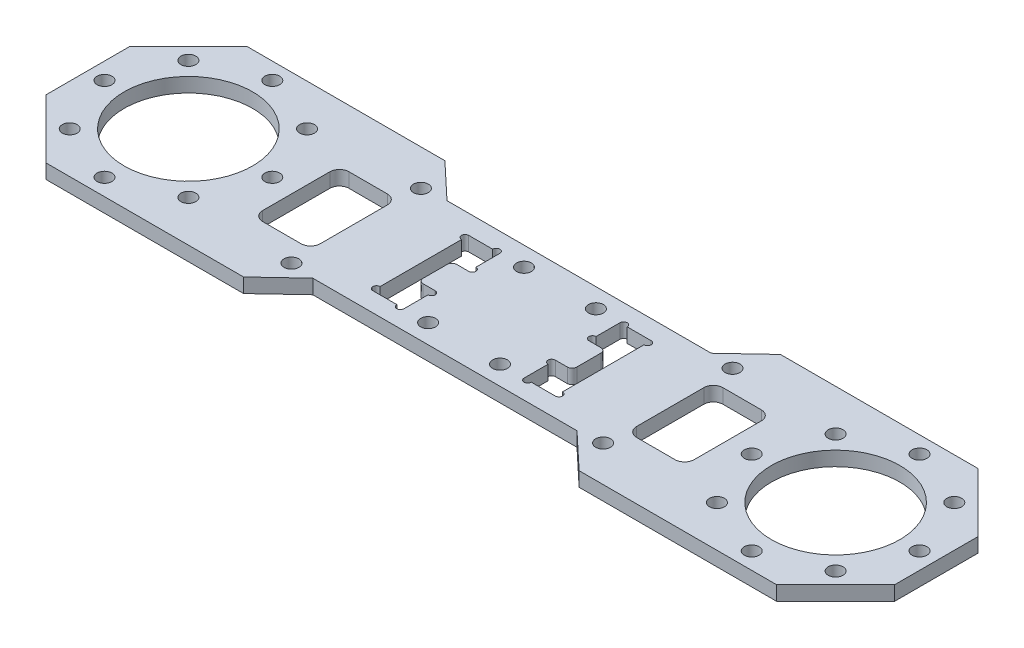
SolidWorks part; units mm, degrees
ref_plane "前视基准面" through (0, 0, 0) normal (0, 0, 1) x (1, 0, 0)
ref_plane "上视基准面" through (0, 0, 0) normal (0, 1, 0) x (1, 0, 0)
ref_plane "右视基准面" through (0, 0, 0) normal (1, 0, 0) x (0, 0, -1)
sketch "草图1" plane through (0, 0, 0) normal (0, 1, 0) x (1, 0, 0)
  line L0 (67.5, 0) -> (-67.5, 0) construction
  line L1 (-67.5, 0) -> (-67.5, 17.5) construction
  line L2 (0, 0) -> (0, 5) construction
  line L4 (88.5, -21) -> (-88.5, -21)
  line L5 (88.5, -21) -> (88.5, 21)
  line L6 (88.5, 21) -> (-88.5, 21)
  line L7 (-88.5, -21) -> (-88.5, 21)
  line L8 (88.5, -21) -> (-88.5, 21) construction
  line L9 (88.5, 21) -> (-88.5, -21) construction
  circle A0 centre (-67.5, 0) radius 17.5 construction
  circle A1 centre (67.5, 0) radius 17.5 construction
  circle A2 centre (-67.5, 17.5) radius 1.55
  circle A3 centre (-55.1256, 12.3744) radius 1.55
  circle A4 centre (-50, 0) radius 1.55
  circle A5 centre (-55.1256, -12.3744) radius 1.55
  circle A6 centre (-67.5, -17.5) radius 1.55
  circle A7 centre (-79.8744, -12.3744) radius 1.55
  circle A8 centre (-85, 0) radius 1.55
  circle A9 centre (-79.8744, 12.3744) radius 1.55
  circle A10 centre (67.5, 17.5) radius 1.55
  circle A11 centre (55.1256, 12.3744) radius 1.55
  circle A12 centre (50, 0) radius 1.55
  circle A13 centre (55.1256, -12.3744) radius 1.55
  circle A14 centre (67.5, -17.5) radius 1.55
  circle A15 centre (79.8744, -12.3744) radius 1.55
  circle A16 centre (85, 0) radius 1.55
  circle A17 centre (79.8744, 12.3744) radius 1.55
  circle A18 centre (-67.5, 0) radius 13.4
  circle A19 centre (67.5, 0) radius 13.4
  point P4 (0, 0)
  dimension "D2" = 35
  dimension "D3" = 3.1
  dimension "D6" = 26.8
  dimension "D7" = 42
  dimension "D1" = 135
  dimension "D5" = 5
  dimension "D8" = 21
  dimension "D4" = 8
extrude "凸台-拉伸1" add sketch "草图1" along normal mid plane 3
sketch "草图3" plane through (0, 1.5, 0) normal (0, 1, 0) x (1, 0, 0)
  line L0 (0, 21) -> (0, -21) construction
  line L1 (12.525, 10) -> (19.025, 10)
  line L2 (12.525, 10) -> (12.525, -10)
  line L3 (12.525, -10) -> (19.025, -10)
  line L4 (19.025, 10) -> (19.025, -10)
  line L5 (88.5, 21) -> (-88.5, 21) construction
  line L6 (-88.5, -21) -> (88.5, -21) construction
  line L9 (-12.525, -10) -> (-19.025, -10)
  line L10 (-19.025, 10) -> (-19.025, -10)
  line L11 (-12.525, 10) -> (-19.025, 10)
  line L12 (-12.525, 10) -> (-12.525, -10)
  point P12 (12.525, 0)
  dimension "D1" = 25.05
  dimension "D3" = 6.5
  dimension "D4" = 20
extrude "切除-拉伸1" cut sketch "草图3" against normal through all
sketch "草图4" plane through (0, 1.5, 0) normal (0, 1, 0) x (1, 0, 0)
  line L0 (-12.525, -10) -> (-12.525, 10) construction
  line L1 (-12.525, 3.5) -> (-16.025, 3.5)
  line L2 (-12.525, 3.5) -> (-12.525, -3.5)
  line L3 (-12.525, -3.5) -> (-16.025, -3.5)
  line L4 (-16.025, 3.5) -> (-16.025, -3.5)
  line L5 (12.525, 10) -> (12.525, -10) construction
  line L6 (12.525, 3.5) -> (16.025, 3.5)
  line L7 (12.525, 3.5) -> (12.525, -3.5)
  line L8 (12.525, -3.5) -> (16.025, -3.5)
  line L9 (16.025, 3.5) -> (16.025, -3.5)
  point P12 (-12.525, 0)
  dimension "D1" = 3.5
  dimension "D2" = 7
extrude "凸台-拉伸2" add sketch "草图4" against normal blind 3
sketch "草图5" plane through (0, 1.5, 0) normal (0, 1, 0) x (1, 0, 0)
  line L0 (12.525, 10) -> (12.525, 3.5) construction
  line L1 (12.525, -3.5) -> (12.525, -10) construction
  line L2 (12.525, -10) -> (19.025, -10) construction
  line L3 (19.025, 10) -> (12.525, 10) construction
  line L4 (19.025, -10) -> (19.025, 10) construction
  line L5 (0, 21) -> (0, -21) construction
  line L6 (88.5, 21) -> (-88.5, 21) construction
  line L7 (-88.5, -21) -> (88.5, -21) construction
  line L8 (-16.025, 3.5) -> (-16.025, -3.5) construction
  line L9 (16.025, -3.5) -> (16.025, 3.5) construction
  circle A0 centre (12.525, 4.25) radius 0.75
  circle A1 centre (12.525, -4.25) radius 0.75
  circle A2 centre (13.275, -10) radius 0.75
  circle A3 centre (13.275, 10) radius 0.75
  circle A4 centre (19.025, 9.25) radius 0.75
  circle A5 centre (19.025, -9.25) radius 0.75
  circle A6 centre (-19.025, -9.25) radius 0.75
  circle A7 centre (-19.025, 9.25) radius 0.75
  circle A8 centre (-13.275, 10) radius 0.75
  circle A9 centre (-13.275, -10) radius 0.75
  circle A10 centre (-12.525, -4.25) radius 0.75
  circle A11 centre (-12.525, 4.25) radius 0.75
  dimension "D1" = 1.5
extrude "切除-拉伸2" cut sketch "草图5" against normal through all
fillet "圆角1" radius 1 4 edges at (16.025, 0, -3.5) (16.025, 0, 3.5) (-16.025, 0, -3.5) (-16.025, 0, 3.5)
sketch "草图6" plane through (0, 1.5, 0) normal (0, 1, 0) x (1, 0, 0)
  line L1 (7.5, -10) -> (-7.5, -10) construction
  line L2 (7.5, -10) -> (7.5, 10) construction
  line L3 (7.5, 10) -> (-7.5, 10) construction
  line L4 (-7.5, -10) -> (-7.5, 10) construction
  line L5 (7.5, -10) -> (-7.5, 10) construction
  line L6 (7.5, 10) -> (-7.5, -10) construction
  line L7 (32.5, -13.5) -> (-32.5, -13.5) construction
  line L8 (32.5, -13.5) -> (32.5, 13.5) construction
  line L9 (32.5, 13.5) -> (-32.5, 13.5) construction
  line L10 (-32.5, -13.5) -> (-32.5, 13.5) construction
  line L11 (32.5, -13.5) -> (-32.5, 13.5) construction
  line L12 (32.5, 13.5) -> (-32.5, -13.5) construction
  circle A0 centre (-32.5, 13.5) radius 1.55
  circle A1 centre (-32.5, -13.5) radius 1.55
  circle A2 centre (-7.5, 10) radius 1.55
  circle A3 centre (-7.5, -10) radius 1.55
  circle A4 centre (7.5, -10) radius 1.55
  circle A5 centre (7.5, 10) radius 1.55
  circle A6 centre (32.5, 13.5) radius 1.55
  circle A7 centre (32.5, -13.5) radius 1.55
  point P0 (0, 0)
  point P5 (0, 0)
  dimension "D5" = 3.1
  dimension "D1" = 20
  dimension "D2" = 15
  dimension "D3" = 27
  dimension "D4" = 65
extrude "切除-拉伸3" cut sketch "草图6" against normal through all and the other way through all
sketch "草图7" plane through (0, -1.5, 0) normal (0, -1, 0) x (1, 0, 0)
  line L0 (0, 21) -> (0, -21) construction
  line L1 (-88.5, 21) -> (88.5, 21) construction
  line L2 (88.5, -21) -> (-88.5, -21) construction
  line L3 (-35, 21) -> (-27.5584, 14)
  line L4 (-27.5584, 14) -> (27.5584, 14)
  line L5 (-35, 21) -> (35, 21)
  line L6 (35, 21) -> (27.5584, 14)
  line L7 (-88.5, 8.6985) -> (-76.1985, 21)
  line L8 (-88.5, -21) -> (-88.5, 21) construction
  line L9 (-76.1985, 21) -> (-88.5, 21)
  line L10 (-88.5, 21) -> (-88.5, 8.6985)
  line L17 (76.1985, 21) -> (88.5, 21)
  line L18 (88.5, 8.6985) -> (76.1985, 21)
  line L19 (88.5, 21) -> (88.5, 8.6985)
  circle A0 centre (-32.5, 13.5) radius 3.75 construction
  circle A1 centre (-67.5, 0) radius 13.4 construction
  point P13 (0, 14)
  dimension "D1" = 7.5
  dimension "D2" = 70
  dimension "D3" = 7
  dimension "D4" = 21
extrude "切除-拉伸4" cut sketch "草图7" against normal through all
mirror "镜向1" about plane through (0, 0, 0) normal (0, 0, 1) of "切除-拉伸4"
sketch "草图8" plane through (0, -1.5, 0) normal (0, -1, 0) x (1, 0, 0)
  line L0 (0, 14) -> (0, -14) construction
  line L1 (-33, -9) -> (-45, -9)
  line L2 (-33, -9) -> (-33, 9)
  line L3 (-33, 9) -> (-45, 9)
  line L4 (-45, -9) -> (-45, 9)
  line L5 (-33, -9) -> (-45, 9) construction
  line L6 (-33, 9) -> (-45, -9) construction
  line L7 (-27.5584, 14) -> (27.5584, 14) construction
  line L8 (-27.5584, -14) -> (27.5584, -14) construction
  line L9 (33, 9) -> (45, 9)
  line L10 (45, -9) -> (45, 9)
  line L11 (33, -9) -> (45, -9)
  line L12 (33, -9) -> (33, 9)
  point P0 (-39, 0)
  point P11 (0, 0)
  dimension "D1" = 78
  dimension "D2" = 12
  dimension "D3" = 18
extrude "切除-拉伸5" cut sketch "草图8" against normal through all
fillet "圆角2" radius 2 8 edges at (33, 0, 9) (45, 0, -9) (33, 0, -9) (45, 0, 9) (-45, 0, 9) (-33, 0, -9) (-45, 0, -9) (-33, 0, 9)
